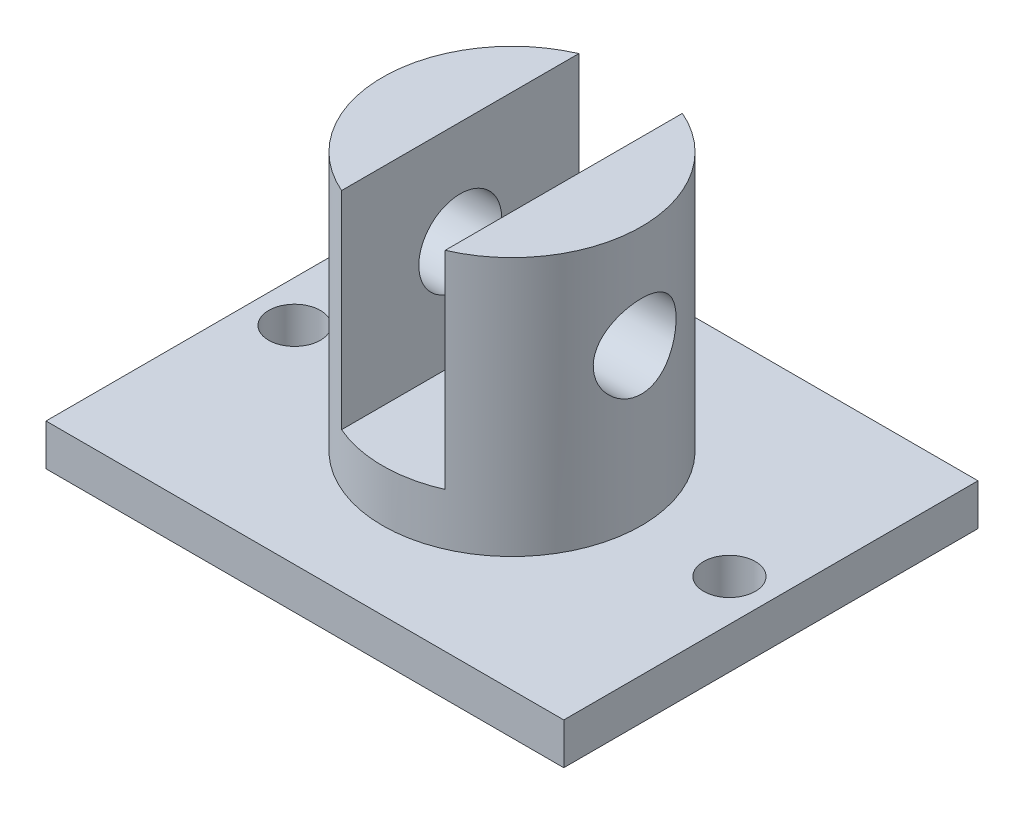
SolidWorks part; units mm, degrees
ref_plane "前视基准面" through (0, 0, 0) normal (0, 0, 1) x (1, 0, 0)
ref_plane "上视基准面" through (0, 0, 0) normal (0, 1, 0) x (1, 0, 0)
ref_plane "右视基准面" through (0, 0, 0) normal (1, 0, 0) x (0, 0, -1)
sketch "草图1" plane through (0, 0, 0) normal (0, 1, 0) x (1, 0, 0)
  line L1 (-25, 20) -> (25, 20)
  line L2 (-25, 20) -> (-25, -20)
  line L3 (-25, -20) -> (25, -20)
  line L4 (25, 20) -> (25, -20)
  line L5 (-25, 20) -> (25, -20) construction
  line L6 (-25, -20) -> (25, 20) construction
  point P0 (0, 0)
  dimension "D1" = 50
  dimension "D2" = 40
extrude "凸台-拉伸1" add sketch "草图1" along normal blind 4
sketch "草图2" plane through (0, 4, 0) normal (0, 1, 0) x (1, 0, 0)
  circle A0 centre (0, 0) radius 12.5
  dimension "D1" = 25
extrude "凸台-拉伸2" add sketch "草图2" along normal blind 25
sketch "草图3" plane through (0, 0, 0) normal (0, 0, 1) x (1, 0, 0)
  line L0 (12.5, 29) -> (-12.5, 29) construction
  line L1 (-5, 29) -> (5, 29)
  line L2 (-5, 29) -> (-5, 9)
  line L3 (-5, 9) -> (5, 9)
  line L4 (5, 29) -> (5, 9)
  line L5 (-5, 29) -> (5, 9) construction
  line L6 (-5, 9) -> (5, 29) construction
  point P0 (0, 19)
  dimension "D1" = 10
  dimension "D2" = 20
extrude "切除-拉伸1" cut sketch "草图3" against normal mid plane 40
sketch "草图4" plane through (0, 0, 0) normal (1, 0, 0) x (0, 0, -1)
  line L0 (11.4564, 29) -> (-11.4564, 29) construction
  circle A0 centre (0, 19) radius 4
  dimension "D1" = 8
  dimension "D2" = 10
extrude "切除-拉伸2" cut sketch "草图4" against normal through all both and the other way through all
sketch "草图5" plane through (0, 4, 0) normal (0, 1, 0) x (1, 0, 0)
  line L3 (21, -20) -> (21, 20)
  line L4 (21, -20) -> (21, 20) construction
  line L5 (-21, 0) -> (15.1711, 0) construction
  line L6 (-21, 20) -> (-21, -20)
  line L7 (-21, 20) -> (-21, -20) construction
  circle A0 centre (-21, 0) radius 2.5
  circle A1 centre (21, 0) radius 2.5
  dimension "D3" = 5
  dimension "D4" = 5
  dimension "D1" = 4
  dimension "D2" = 4
extrude "切除-拉伸3" cut sketch "草图5" against normal blind 10
